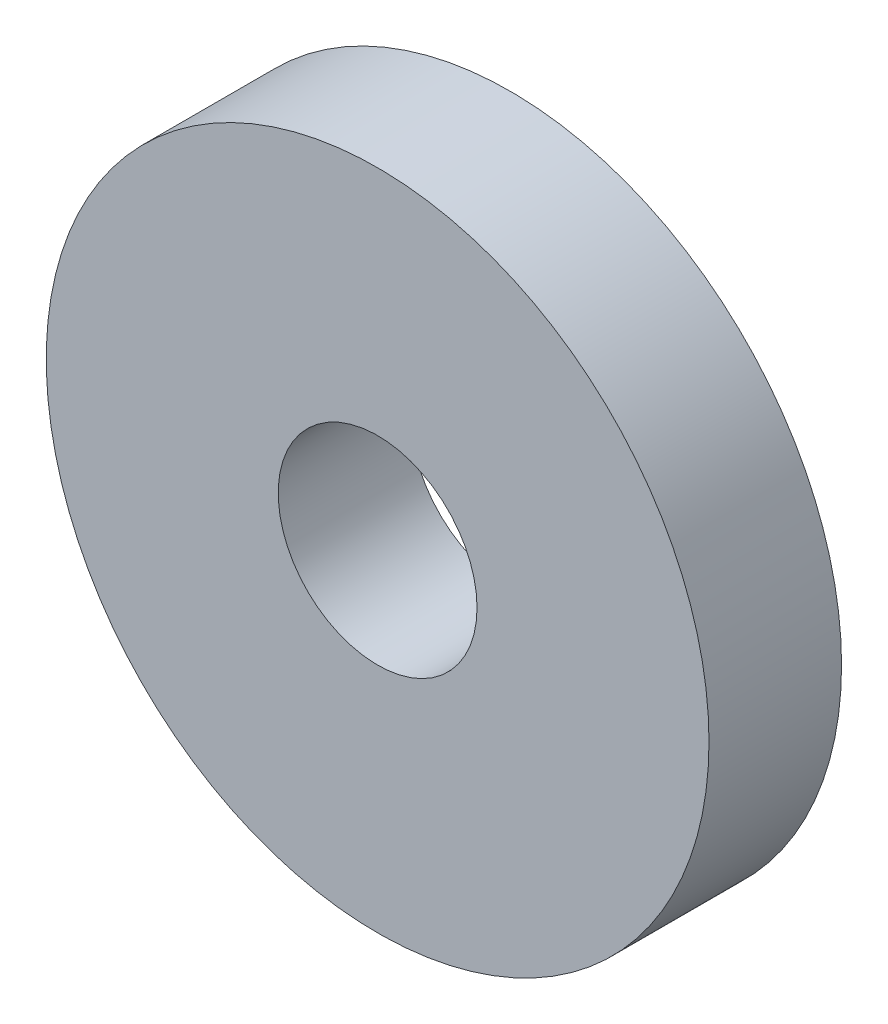
SolidWorks part; units mm, degrees
ref_plane "Front Plane" through (0, 0, 0) normal (0, 0, 1) x (1, 0, 0)
ref_plane "Top Plane" through (0, 0, 0) normal (0, 1, 0) x (1, 0, 0)
ref_plane "Right Plane" through (0, 0, 0) normal (1, 0, 0) x (0, 0, -1)
sketch "Sketch1" plane through (0, 0, 0) normal (0, 0, 1) x (1, 0, 0)
  circle A0 centre (0, 0) radius 7.5
  circle A1 centre (0, 0) radius 2.25
  dimension "D1" = 15
  dimension "D2" = 4.5
extrude "Boss-Extrude1" add sketch "Sketch1" along normal blind 3
